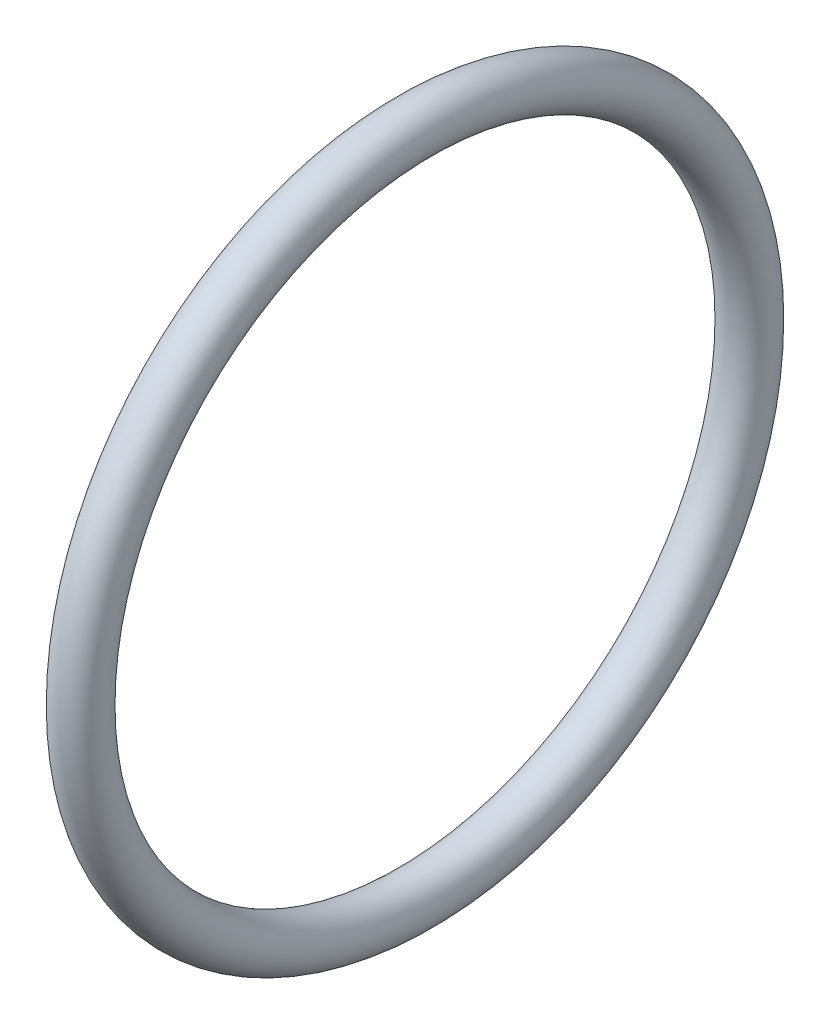
SolidWorks part; units mm, degrees
ref_plane "Front Plane" through (0, 0, 0) normal (0, 0, 1) x (1, 0, 0)
ref_plane "Top Plane" through (0, 0, 0) normal (0, 1, 0) x (1, 0, 0)
ref_plane "Right Plane" through (0, 0, 0) normal (1, 0, 0) x (0, 0, -1)
sketch "Sketch1" [suppressed] plane through (0, 0, 0) normal (0, 0, 1) x (1, 0, 0)
  line L0 (-43.7166, 0) -> (79.6876, 0) construction
  line L2 (0, -13.462) -> (1.524, -13.462)
  line L3 (0, -13.462) -> (0, -18.161)
  line L4 (0, -18.161) -> (1.524, -18.161)
  line L5 (1.524, -13.462) -> (1.524, -18.161)
  dimension "A" = 28.194
  dimension "B" = 33.528
  dimension "C" = 2.032
revolve "Revolve1" [suppressed] add sketch "Sketch1" angle 360 about L0
sketch "Sketch2" plane through (0, 0, 0) normal (0, 0, 1) x (1, 0, 0)
  line L0 (-34.685, 0) -> (47.6686, 0) construction
  circle A0 centre (2.54, -13.97) radius 1.016
  dimension "D1" = 2.54
  dimension "E" = 2.032
  dimension "D" = 25.908
revolve "Revolve3" add sketch "Sketch2" angle 360 about L0
